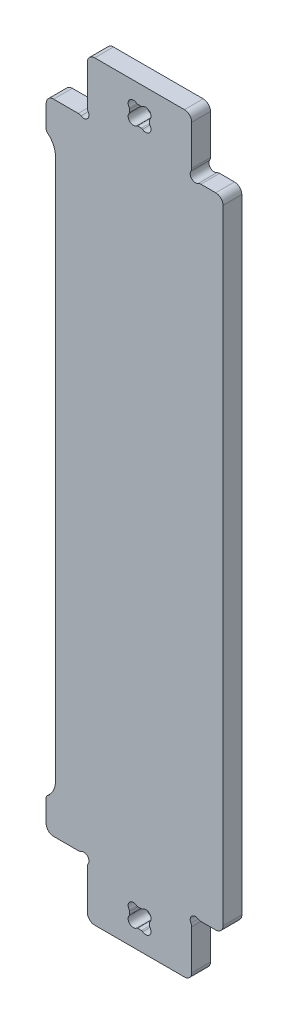
SolidWorks part; units mm, degrees
ref_plane "Plan de face" through (0, 0, 0) normal (0, 0, 1) x (1, 0, 0)
ref_plane "Plan de dessus" through (0, 0, 0) normal (0, 1, 0) x (1, 0, 0)
ref_plane "Plan de droite" through (0, 0, 0) normal (1, 0, 0) x (0, 0, -1)
sketch "Esquisse2" plane through (0, 0, 0) normal (0, 0, 1) x (1, 0, 0)
  line L0 (0, 54) -> (-56.1998, -2.1998) construction
  line L1 (0, 0) -> (100, 0)
  line L2 (0, 0) -> (0, 45.2544)
  line L3 (-30.4949, 360) -> (-30.4949, 101.2337)
  line L4 (100, 0) -> (100, 45.2544)
  line L5 (130, 360) -> (-30.4949, 360)
  line L6 (100, 54) -> (107.0711, 46.9289) construction
  line L7 (-8.7456, 54) -> (-39.4949, 54)
  line L8 (-39.4949, 82.7404) -> (-39.4949, 54)
  line L10 (-39.9949, 61) -> (-39.9949, 659) construction
  line L11 (108.7456, 54) -> (130, 54)
  line L12 (130, 360) -> (130, 54)
  arc A0 (0.7322, 47.8594) -> (-6.1406, 54.7322) centre (-3.5355, 50.4645) ccw
  arc A1 (106.1406, 54.7322) -> (99.2678, 47.8594) centre (103.5355, 50.4645) ccw
  arc A2 (-38.5375, 84.7078) -> (-30.4949, 101.2337) centre (-51.4949, 101.2337) ccw
  arc A3 (106.1406, 54.7322) -> (108.7456, 54) centre (108.7456, 59) ccw
  arc A4 (100, 45.2544) -> (99.2678, 47.8594) centre (95, 45.2544) ccw
  arc A5 (-6.1406, 54.7322) -> (-8.7456, 54) centre (-8.7456, 59) cw
  arc A6 (0, 45.2544) -> (0.7322, 47.8594) centre (5, 45.2544) cw
  arc A7 (-38.5375, 84.7078) -> (-39.4949, 82.7404) centre (-36.9949, 82.7404) ccw
  point P32 (-39.4949, 84)
  dimension "D3" = 45
  dimension "D4" = 5
  dimension "D11" = 5
  dimension "D12" = 2.5
  dimension "D1" = 100
  dimension "D5" = 45
  dimension "D2" = 360
  dimension "D6" = 12
  dimension "D7" = 54
  dimension "D8" = 9
  dimension "D9" = 30
  dimension "D10" = 30
  dimension "D13" = 0.5
extrude "Boss.-Extru.2" add sketch "Esquisse2" along normal blind 18
sketch "Esquisse1" plane through (0, 0, 0) normal (0, 0, 1) x (1, 0, 0)
  line L0 (50, 0) -> (50, 18) construction
  line L1 (0, 0) -> (100, 0) construction
  line L3 (59.5, 28.2488) -> (59.5, 25.7512)
  line L4 (48.2512, 36) -> (51.7488, 36)
  line L5 (40.5, 27) -> (59.5, 27) construction
  line L6 (40.5, 28.2488) -> (40.5, 25.7512)
  line L7 (48.2512, 18) -> (51.7488, 18)
  line L8 (-39.4949, 54) -> (-8.7456, 54) construction
  line L9 (40.5, 18) -> (50, 27.5) construction
  arc A0 (40.1123, 24.6353) -> (47.1353, 17.6123) centre (44.0355, 21.5355) ccw
  arc A1 (47.1353, 17.6123) -> (48.2512, 18) centre (48.2512, 16.2) cw
  arc A2 (40.1123, 24.6353) -> (40.5, 25.7512) centre (38.7, 25.7512) ccw
  arc A3 (52.8647, 17.6123) -> (51.7488, 18) centre (51.7488, 16.2) ccw
  arc A4 (59.8877, 24.6353) -> (52.8647, 17.6123) centre (55.9645, 21.5355) cw
  arc A5 (59.8877, 24.6353) -> (59.5, 25.7512) centre (61.3, 25.7512) cw
  arc A6 (59.8877, 29.3647) -> (59.5, 28.2488) centre (61.3, 28.2488) ccw
  arc A7 (59.8877, 29.3647) -> (52.8647, 36.3877) centre (55.9645, 32.4645) ccw
  arc A8 (52.8647, 36.3877) -> (51.7488, 36) centre (51.7488, 37.8) cw
  arc A9 (47.1353, 36.3877) -> (48.2512, 36) centre (48.2512, 37.8) ccw
  arc A10 (40.1123, 29.3647) -> (47.1353, 36.3877) centre (44.0355, 32.4645) cw
  arc A11 (40.1123, 29.3647) -> (40.5, 28.2488) centre (38.7, 28.2488) cw
  point P2 (50, 0)
  point P21 (50, 18)
  dimension "D7" = 5
  dimension "D1" = 1.8
  dimension "D3" = 45
  dimension "D5" = 9
  dimension "D6" = 9.5
  dimension "D2" = 18
extrude "Enlèv. mat.-Extru.1" cut sketch "Esquisse1" along normal through all
fillet "Congé1" radius 7 4 edges at (100, 0, 9) (0, 0, 9) (-39.4949, 54, 9) (130, 54, 9)
mirror "Symétrie1" about plane through (130, 360, 18) normal (0, -1, 0) of bodies 104
equation "\"tool_diameter\"=9"
equation "\"D1@Boss.-Extru.2\" = \"material_thickness\""
equation "\"D7@Esquisse1\" = \"tool_diameter\" / 2 + \"hole_clearance\""
equation "\"D6@Esquisse1\" = \"material_thickness\" / 2 + \"clearance\""
equation "\"fillet\"=7"
equation "\"D5@Esquisse1\" = \"material_thickness\" / 2"
equation "\"D4@Esquisse2\"= \"tool_diameter\" / 2 + \"hole_clearance\""
equation "\"D1@Esquisse1\"=\"material_thickness\"/10"
equation "\"D8@Esquisse2\" = \"material_thickness\" / 2"
equation "\"D6@Esquisse2\" = \"material_thickness\" * 2 / 3"
equation "\"D1@Congé1\"=\"fillet\""
equation "\"clearance\"=0.5"
equation "\"D7@Esquisse2\" = \"material_thickness\" * 3"
equation "\"outer_slot\"=0.5"
equation "\"hole_clearance\"=0.5"
equation "\"material_thickness\"=18"
equation "\"D11@Esquisse2\"=\"D4@Esquisse2\""
equation "\"D12@Esquisse2\"=\"D4@Esquisse2\"/2"
equation "\"D2@Esquisse1\"=\"material_thickness\""
equation "\"D13@Esquisse2\"=\"clearance\""
equation "\"string\"= 2 * \"tool_diameter\" / 2 * cos ( 45deg )"
equation "\"angle\"= IIF ( \"string\" < \"limit\" , 45 , ( 180 - 2 * arcsin ( \"ThicknessVStool_dia\" ) ) / 2 )"
equation "\"limit\"= \"material_thickness\" / 2 * 9 / 10"
equation "\"ThicknessVStool_dia\"= IIF ( \"limit\" / \"tool_diameter\" > 1 , 1 , \"limit\" / \"tool_diameter\" )"
equation "\"D3@Esquisse1\"=\"angle\""
